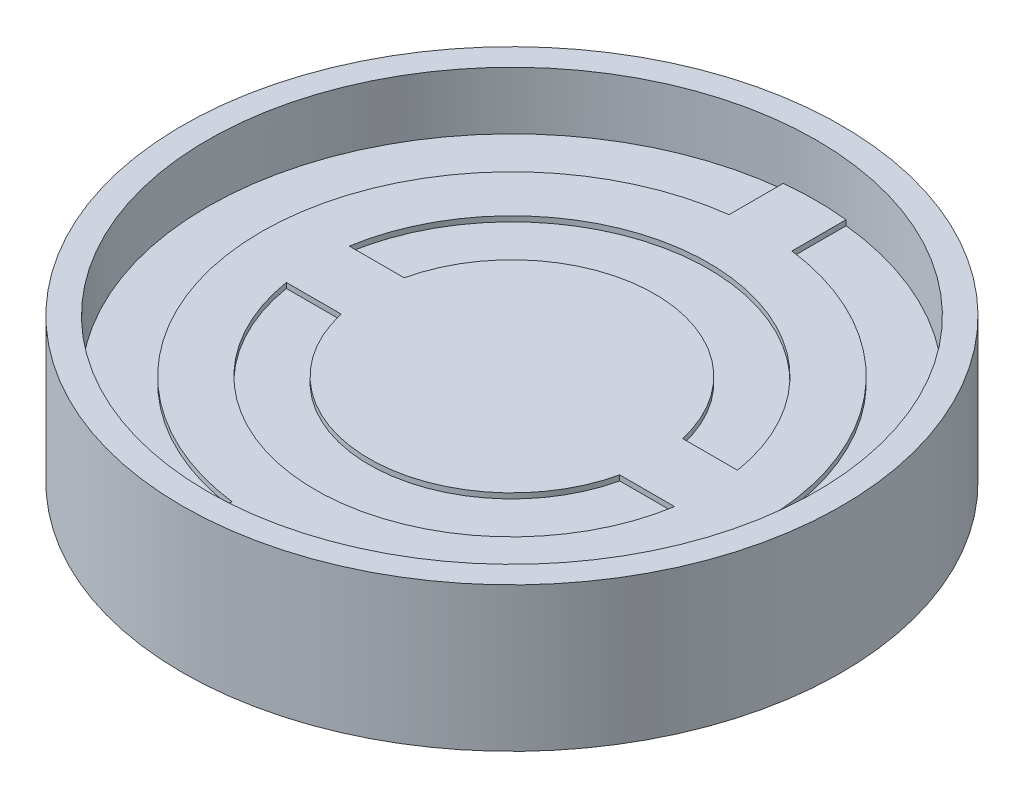
SolidWorks part; units mm, degrees
material "ABS PC"
ref_plane "Front Plane" through (0, 0, 0) normal (0, 0, 1) x (1, 0, 0)
ref_plane "Top Plane" through (0, 0, 0) normal (0, 1, 0) x (1, 0, 0)
ref_plane "Right Plane" through (0, 0, 0) normal (1, 0, 0) x (0, 0, -1)
sketch "Sketch1" plane through (0, 0, 0) normal (0, 1, 0) x (1, 0, 0)
  circle A0 centre (0, 0) radius 15.9639
  dimension "D1" = 31.9278
extrude "Boss-Extrude1" add sketch "Sketch1" along normal mid plane 6.985
sketch "Sketch2" plane through (0, 3.4925, 0) normal (0, 1, 0) x (1, 0, 0)
  circle A0 centre (0, 0) radius 14.7447
  circle A1 centre (0, 0) radius 15.9639 construction
  dimension "D1" = 1.2192
extrude "Cut-Extrude1" cut sketch "Sketch2" against normal blind 2.794
sketch "Sketch3" plane through (0, 0.6985, 0) normal (0, 1, 0) x (1, 0, 0)
  line L0 (6.9152, 0) -> (9.525, 0) construction
  line L1 (9.525, 0) -> (12.1348, 0) construction
  line L2 (12.1348, 0) -> (14.7447, 0) construction
  line L3 (-1.524, -12.0388) -> (1.524, -15.891) construction
  line L4 (-1.524, 15.891) -> (1.524, 15.891)
  line L5 (-1.524, 15.891) -> (-1.524, 12.0388)
  line L6 (-1.524, 12.0388) -> (1.524, 12.0388)
  line L7 (1.524, 15.891) -> (1.524, 12.0388)
  line L8 (-1.524, 15.891) -> (1.524, 12.0388) construction
  line L9 (-1.524, 12.0388) -> (1.524, 15.891) construction
  line L10 (-12.0388, 1.524) -> (-6.7451, 1.524)
  line L11 (-12.0388, 1.524) -> (-12.0388, -1.524)
  line L12 (-12.0388, -1.524) -> (-6.7451, -1.524)
  line L13 (-6.7451, 1.524) -> (-6.7451, -1.524)
  line L14 (-12.0388, 1.524) -> (-6.7451, -1.524) construction
  line L15 (-12.0388, -1.524) -> (-6.7451, 1.524) construction
  line L16 (-1.524, -15.891) -> (1.524, -12.0388) construction
  line L17 (1.524, -15.891) -> (1.524, -12.0388)
  line L18 (-1.524, -12.0388) -> (1.524, -12.0388)
  line L19 (-1.524, -15.891) -> (-1.524, -12.0388)
  line L20 (-1.524, -15.891) -> (1.524, -15.891)
  line L21 (0, 0) -> (0, 6.9152) construction
  line L22 (12.0388, -1.524) -> (6.7451, 1.524) construction
  line L23 (12.0388, 1.524) -> (6.7451, -1.524) construction
  line L24 (6.7451, 1.524) -> (6.7451, -1.524)
  line L25 (12.0388, -1.524) -> (6.7451, -1.524)
  line L26 (12.0388, 1.524) -> (12.0388, -1.524)
  line L27 (12.0388, 1.524) -> (6.7451, 1.524)
  circle A0 centre (0, 0) radius 6.9152
  circle A1 centre (0, 0) radius 9.525
  circle A2 centre (0, 0) radius 12.1348
  circle A3 centre (0, 0) radius 14.7447 construction
  circle A5 centre (0, 0) radius 15.9639 construction
  point P7 (0, 13.9649)
  point P17 (-9.3919, 0)
  point P28 (0, -13.9649)
  point P34 (9.3919, 0)
  circle M4 centre (0, 0) radius 14.7447
  dimension "D1" = 13.8303
  dimension "D2" = 19.05
  dimension "D3" = 24.2697
  dimension "D4" = 3.048
extrude "Boss-Extrude2" add sketch "Sketch3" along normal blind 0.254 contours L24 A0 L13 | L18 A2 L25 A1 L12 | L27 A2 L6 L10 A1 | A2 L7 L5 M4 | L10 A1 L12 A0 | L25 A1 L27 A0 | A2 L19 L17 M4 | A1 L10 L11 L12 | A1 L25 L26 L27 | L26 A2 | L24 A0 | L13 A0 | L11 A2 | L18 A2 | L6 A2
mirror "Mirror1" about plane through (0, 0, 0) normal (0, 1, 0) of "Boss-Extrude2", "Cut-Extrude1"
